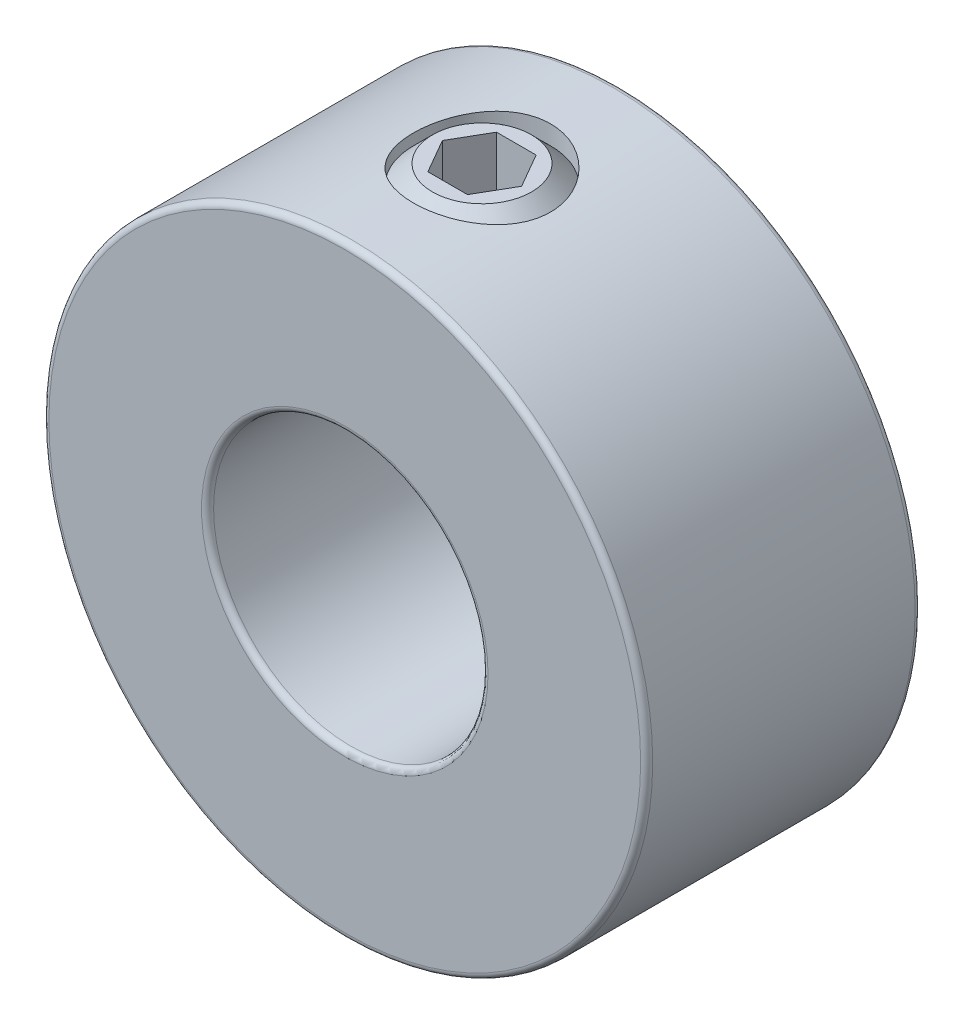
SolidWorks part; units mm, degrees
ref_plane "Front Plane" through (0, 0, 0) normal (0, 0, 1) x (1, 0, 0)
ref_plane "Top Plane" through (0, 0, 0) normal (0, 1, 0) x (1, 0, 0)
ref_plane "Right Plane" through (0, 0, 0) normal (1, 0, 0) x (0, 0, -1)
sketch "Sketch1" plane through (0, 0, 0) normal (0, 0, 1) x (1, 0, 0)
  circle A0 centre (0, 0) radius 11
  circle A1 centre (0, 0) radius 5
  point P4 (11, 0)
  point P5 (0, 11)
  dimension "Bore Dia" = 10
  dimension "OD" = 22
extrude "Extrude1" add sketch "Sketch1" along normal blind 10
ref_plane "Plane1" through (0, 11, 0) normal (0, 1, 0) x (-1, 0, 0)
sketch "Sketch2" plane through (0, 11, 0) normal (0, 1, 0) x (-1, 0, 0)
  line L0 (0, 0) -> (0, 10) construction
  line L2 (11, 10) -> (-11, 10) construction
  circle A0 centre (0, 5) radius 2.5
  dimension "Set Screw Dia" = 5
extrude "Cut-Extrude1" cut sketch "Sketch2" against normal up to surface (11 mm away) up to plane "Top Plane"
ref_plane "Plane2" through (0, 0, 5) normal (0, 0, 1) x (1, 0, 0)
sketch "Sketch3" plane through (0, 0, 5) normal (0, 0, 1) x (1, 0, 0)
  line L0 (-1.8042, 11) -> (-2.5, 10.3042)
  line L1 (0, 7.0825) -> (0, 11)
  line L2 (-0.625, 6) -> (-1.8042, 6)
  line L3 (-2.5, 6.6958) -> (-2.5, 10.3042)
  line L4 (0, 11) -> (-1.8042, 11)
  line L5 (0, 6) -> (0, 0) construction
  line L6 (-2.5, 10.3042) -> (0, 10.3042) construction
  line L7 (0, 7.0825) -> (-0.625, 6)
  line L8 (-1.8042, 6) -> (-2.5, 6.6958)
  point P1 (-0.625, 6)
  dimension "D1" = 3.6084
  dimension "Screw Length" = 5
  dimension "D2" = 45
  dimension "D3" = 5
  dimension "D4" = 45
  dimension "D5" = 60
  dimension "D7" = 2.5
  dimension "D8" = 0.625
revolve "Revolve1" add sketch "Sketch3" angle 360 about L1
sketch "Sketch4" plane through (0, 11, 0) normal (0, 1, 0) x (0, 0, -1)
  line L0 (-5, 1.4434) -> (-5, -1.4434) construction
  line L1 (-5, 1.4434) -> (-6.25, 0.7217)
  line L2 (-6.25, 0.7217) -> (-6.25, -0.7217)
  line L3 (-6.25, -0.7217) -> (-5, -1.4434)
  line L4 (-5, -1.4434) -> (-3.75, -0.7217)
  line L5 (-3.75, -0.7217) -> (-3.75, 0.7217)
  line L6 (-3.75, 0.7217) -> (-5, 1.4434)
  circle A0 centre (-5, 0) radius 1.25 construction
  circle A1 centre (-5, 0) radius 1.4434 construction
  dimension "D1" = 2.8868
  dimension "Hex" = 2.5
extrude "Cut-Extrude2" cut sketch "Sketch4" against normal blind 2
fillet "Fillet1" radius 0.22 4 edges at (5, 0, 0) (5, 0, 10) (11, 0, 0) (11, 0, 10)
equation "\"D3@Sketch3\" = \"Set Screw Dia@Sketch2\""
equation "\"D1@Fillet1\" = \"OD@Sketch1\"*.01"
equation "\"D1@Sketch3\" = \"D1@Sketch4\"*1.25"
equation "\"D1@Cut-Extrude2\" = \"Hex@Sketch4\"*.8"
equation "\"D8@Sketch3\" = \"D7@Sketch3\"/4"
